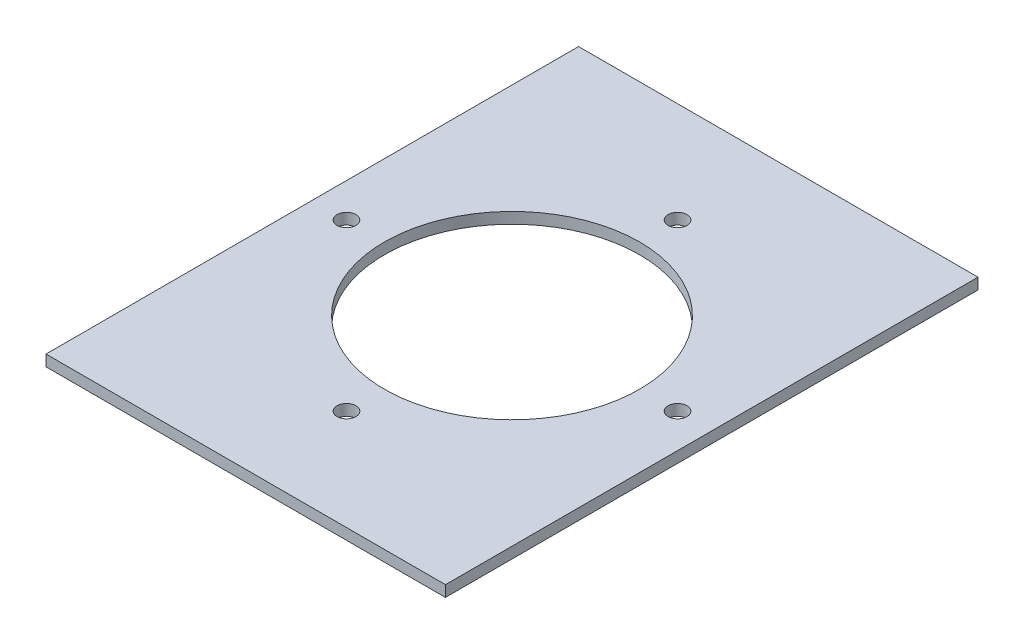
SolidWorks part; units mm, degrees
material "1.0553 (S355J0)"
ref_plane "Płaszczyzna przednia" through (0, 0, 0) normal (0, 0, 1) x (1, 0, 0)
ref_plane "Płaszczyzna górna" through (0, 0, 0) normal (0, 1, 0) x (1, 0, 0)
ref_plane "Płaszczyzna prawa" through (0, 0, 0) normal (1, 0, 0) x (0, 0, -1)
sketch "Szkic1" plane through (0, 0, 0) normal (0, 1, 0) x (1, 0, 0)
  line L1 (-90, -120) -> (90, -120)
  line L2 (-90, -120) -> (-90, 120)
  line L3 (-90, 120) -> (90, 120)
  line L4 (90, -120) -> (90, 120)
  point P4 (0, 120)
  point P6 (90, 0)
  dimension "D4" = 180
  dimension "D5" = 240
extrude "Dodanie-wyciągnięcie1" add sketch "Szkic1" along normal blind 5
sketch "Szkic2" plane through (0, 0, 0) normal (0, 1, 0) x (1, 0, 0)
  circle A0 centre (0, 0) radius 57.5
  circle A1 centre (0, 74.6) radius 4.25
  dimension "D1" = 115
  dimension "D3" = 8.5
  dimension "D2" = 74.6
extrude "Wytnij-wyciągnięcie1" cut sketch "Szkic2" along normal blind 43
pattern_circular "Szyk kołowy1" count 4 every 90 about axis through (0, 0, 0) along (0, 1, 0) of "Wytnij-wyciągnięcie1"
sketch "Szkic3" [suppressed] plane through (0, 5, 0) normal (0, 1, 0) x (1, 0, 0)
  circle A0 centre (0, -53) radius 5.25
  circle A1 centre (0, 0) radius 37.5
  dimension "D1" = 10.5
  dimension "D3" = 75
  dimension "D2" = 53
extrude "Wytnij-wyciągnięcie2" [suppressed] cut sketch "Szkic3" against normal blind 10
pattern_circular "Szyk kołowy2" [suppressed] count 4 every 90
